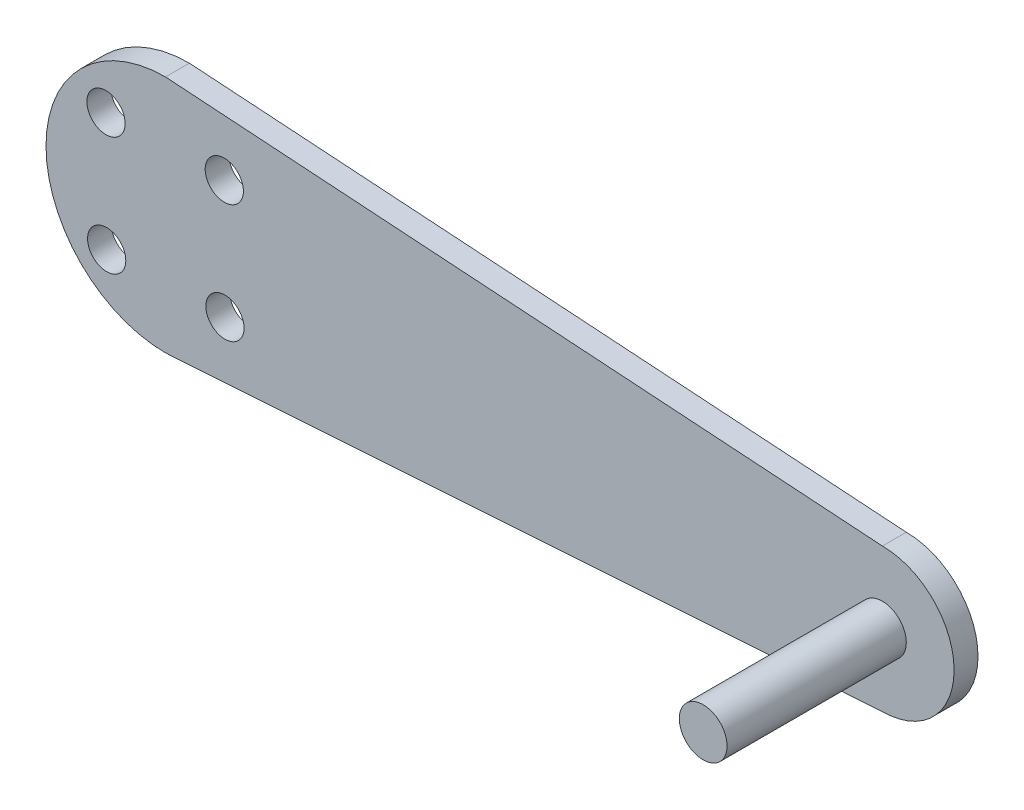
SolidWorks part; units mm, degrees
material "1060 Alloy"
ref_plane "Front Plane" through (0, 0, 0) normal (0, 0, 1) x (1, 0, 0)
ref_plane "Top Plane" through (0, 0, 0) normal (0, 1, 0) x (1, 0, 0)
ref_plane "Right Plane" through (0, 0, 0) normal (1, 0, 0) x (0, 0, -1)
sketch "Sketch1" plane through (0, 0, 0) normal (0, 0, 1) x (1, 0, 0)
  line L0 (0, 10) -> (60, 6)
  line L1 (0, -10) -> (60, -6)
  circle A0 centre (0, 0) radius 10
  circle A1 centre (60, 0) radius 6
  dimension "D1" = 20
  dimension "D2" = 12
  dimension "D3" = 60
extrude "Boss-Extrude1" add sketch "Sketch1" along normal blind 2 contours A1 L0 A0 L1 | A1 | L0 A0 L1
sketch "Sketch2" plane through (0, 0, 2) normal (0, 0, 1) x (1, 0, 0)
  line L0 (0, 10) -> (0, -10) construction
  line L1 (-4.9774, 4.9219) -> (0, 0) construction
  circle A0 centre (-4.9774, 4.9219) radius 1.6
  circle A1 centre (4.9219, 4.9774) radius 1.6
  circle A2 centre (4.9774, -4.9219) radius 1.6
  circle A3 centre (-4.9219, -4.9774) radius 1.6
  point P17 (0, 0)
  dimension "D1" = 4
extrude "Cut-Extrude1" cut sketch "Sketch2" against normal blind 10 contours A0 | A1 | A2 | A3
sketch "Sketch3" plane through (0, 0, 2) normal (0, 0, 1) x (1, 0, 0)
  line L0 (60, 6) -> (60, -6) construction
  arc A0 (60, -6) -> (60, 6) centre (60, 0) ccw construction
  circle A1 centre (60, 0) radius 2
extrude "Boss-Extrude2" add sketch "Sketch3" along normal blind 15
